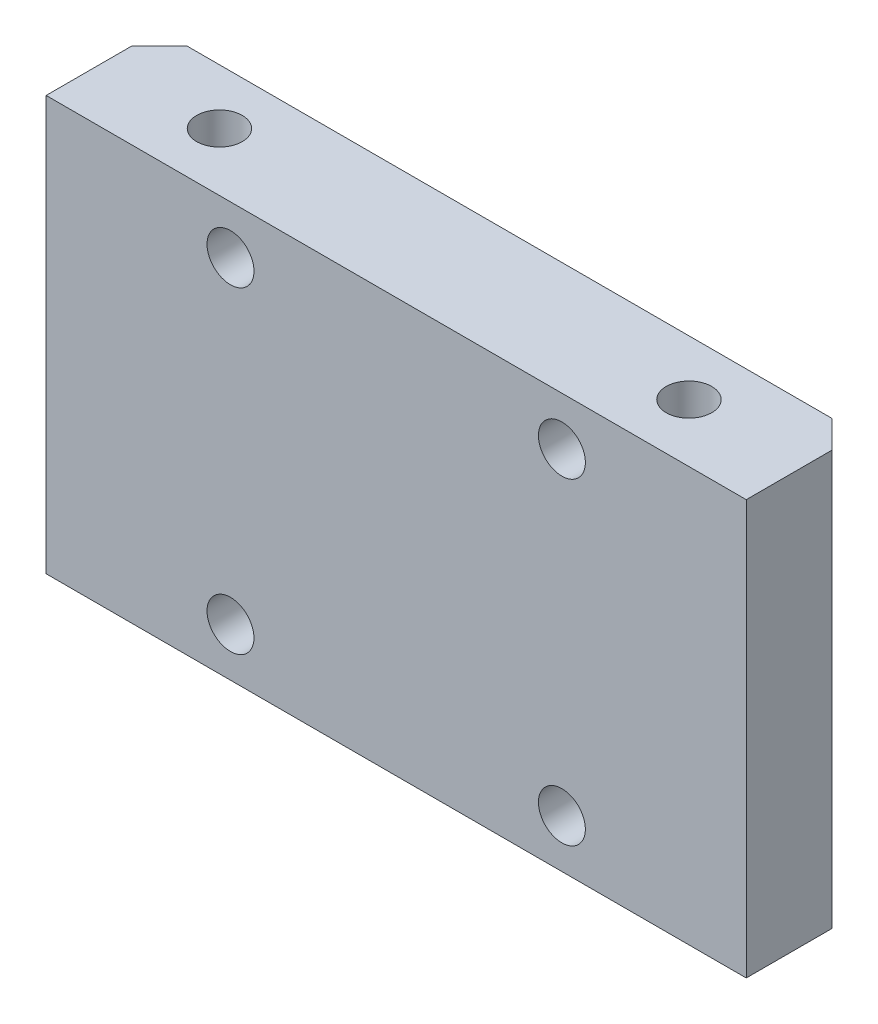
SolidWorks part; units mm, degrees
ref_plane "前视基准面" through (0, 0, 0) normal (0, 0, 1) x (1, 0, 0)
ref_plane "上视基准面" through (0, 0, 0) normal (0, 1, 0) x (1, 0, 0)
ref_plane "右视基准面" through (0, 0, 0) normal (1, 0, 0) x (0, 0, -1)
ref_plane "基准面4" through (0, 0, 449.8) normal (0, 0, -1) x (-1, 0, 0)
sketch "草图1" plane through (0, 0, 449.8) normal (0, 0, -1) x (-1, 0, 0)
  line L0 (-285.35, 255) -> (-285.35, 225)
  line L1 (-285.35, 225) -> (-234.65, 225)
  line L2 (-234.65, 225) -> (-234.65, 255)
  line L3 (-234.65, 255) -> (-285.35, 255)
extrude "凸台-拉伸1" add sketch "草图1" against normal blind 8.2
hole_wizard "Ø3.3 (3.3) 直径孔1" positions "草图3" profile "草图2" hole size "Ø3.3" standard "ANSI Metric"
sketch "草图3" plane through (0, 225, 0) normal (0, -1, 0) x (-1, 0, 0)
  point P0 (-277, -453.8)
  point P1 (-243, -453.8)
sketch "草图2" plane through (277, 225, 453.8) normal (1, 0, 0) x (0, 0, -1)
  line L0 (0, 0) -> (0, 30)
  line L1 (0, 30) -> (1.65, 30)
  line L2 (1.65, 30) -> (1.65, 0)
  line L5 (1.65, 0) -> (0, 0)
  line L11 (0, -6.35) -> (0, 107.95) construction
  dimension "通孔孔直径" = 3.3
  dimension "通孔孔深度" = 30
hole_wizard "Ø3.4 (3.4) 直径孔1" positions "草图5" profile "草图4" hole size "Ø3.4" standard "ANSI Metric"
sketch "草图5" plane through (0, 0, 449.8) normal (0, 0, -1) x (-1, 0, 0)
  point P0 (-272, 251.5)
  point P1 (-272, 228.5)
sketch "草图4" plane through (272, 251.5, 449.8) normal (1, 0, 0) x (0, 1, 0)
  line L0 (0, 0) -> (0, 8.2)
  line L1 (0, 8.2) -> (1.7, 8.2)
  line L2 (1.7, 8.2) -> (1.7, 0)
  line L5 (1.7, 0) -> (0, 0)
  line L11 (0, -6.35) -> (0, 107.95) construction
  dimension "通孔孔直径" = 3.4
  dimension "通孔孔深度" = 8.2
hole_wizard "Ø3.4 (3.4) 直径孔2" positions "草图7" profile "草图6" hole size "Ø3.4" standard "ANSI Metric"
sketch "草图7" plane through (0, 0, 458) normal (0, 0, 1) x (1, 0, 0)
  point P0 (248, 251.5)
  point P1 (248, 228.5)
sketch "草图6" plane through (248, 251.5, 458) normal (1, 0, 0) x (0, -1, 0)
  line L0 (0, 0) -> (0, 8.2)
  line L1 (0, 8.2) -> (1.7, 8.2)
  line L2 (1.7, 8.2) -> (1.7, 0)
  line L5 (1.7, 0) -> (0, 0)
  line L11 (0, -6.35) -> (0, 107.95) construction
  dimension "通孔孔直径" = 3.4
  dimension "通孔孔深度" = 8.2
chamfer "倒角1" distance 1.8 angle 45 4 edges at (270.3, 228.5, 449.8) (249.7, 251.5, 449.8) (270.3, 251.5, 449.8) (249.7, 228.5, 449.8)
chamfer "倒角2" distance 2 angle 45 2 edges at (285.35, 240, 449.8) (234.65, 240, 449.8)
